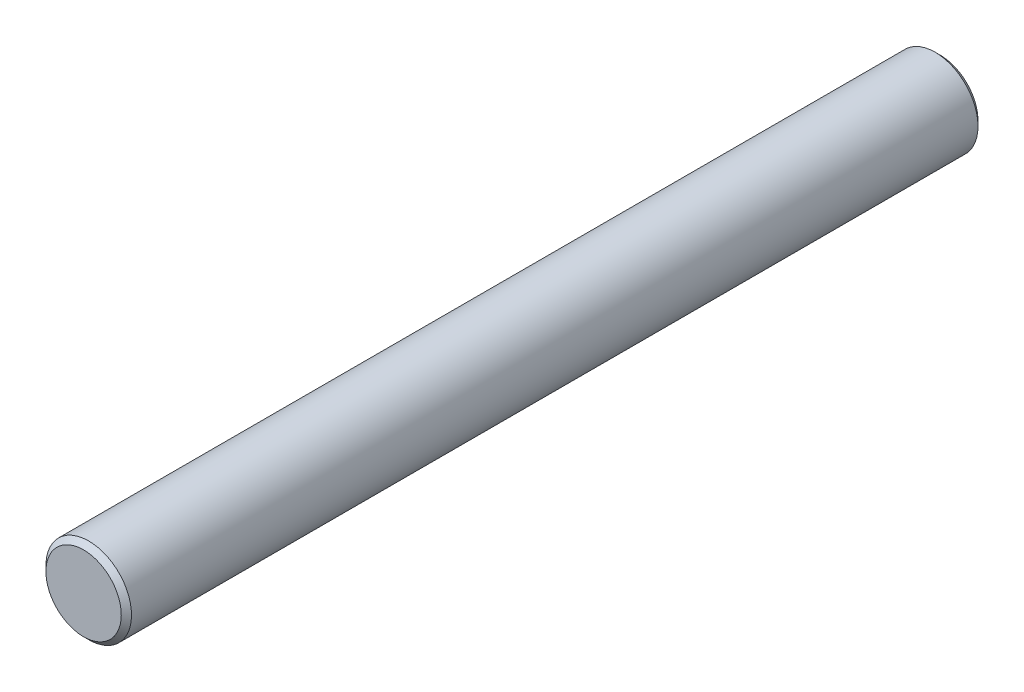
SolidWorks part; units mm, degrees
ref_plane "Front Plane" through (0, 0, 0) normal (0, 0, 1) x (1, 0, 0)
ref_plane "Top Plane" through (0, 0, 0) normal (0, 1, 0) x (1, 0, 0)
ref_plane "Right Plane" through (0, 0, 0) normal (1, 0, 0) x (0, 0, -1)
sketch "Sketch2" plane through (0, 0, 0) normal (0, 0, 1) x (1, 0, 0)
  circle A0 centre (0, 0) radius 3.175
extrude "Boss-Extrude1" add sketch "Sketch2" against normal blind 62.81
sketch "Sketch3" plane through (0, 0, 0) normal (0, 0, 1) x (1, 0, 0)
  circle A0 centre (0, 0) radius 3.175
extrude "Boss-Extrude2" add sketch "Sketch3" along normal blind 0.38 draft 45
sketch "Sketch4" plane through (0, 0, -62.81) normal (0, 0, -1) x (-1, 0, 0)
  circle A0 centre (0, 0) radius 3.175
extrude "Boss-Extrude3" add sketch "Sketch4" along normal blind 0.38 draft 45
